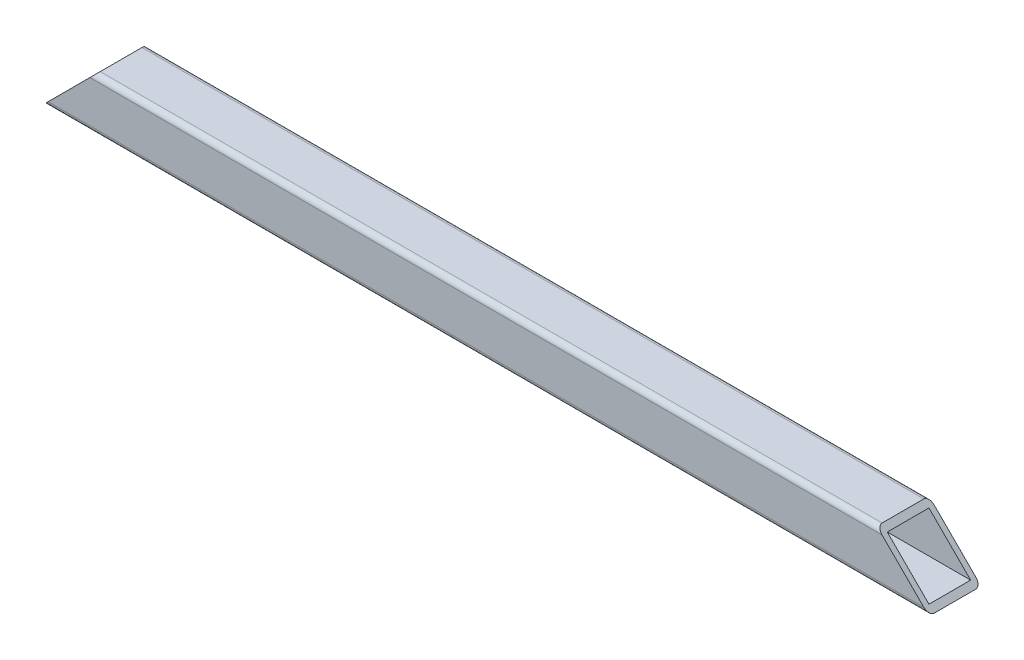
SolidWorks part; units mm, degrees
ref_plane "Front Plane" through (0, 0, 0) normal (0, 0, 1) x (1, 0, 0)
ref_plane "Top Plane" through (0, 0, 0) normal (0, 1, 0) x (1, 0, 0)
ref_plane "Right Plane" through (0, 0, 0) normal (1, 0, 0) x (0, 0, -1)
sketch "Sketch1" plane through (0, 0, 0) normal (0, 0, 1) x (1, 0, 0)
  line L0 (-610.1, -1100) -> (-610.1, 0) construction
  line L1 (-269.9, -1100) -> (-610.1, -1100)
  line L2 (-269.9, -1100) -> (-269.9, -1080)
  line L3 (-269.9, -1080) -> (-610.1, -1080)
  line L4 (-610.1, -1100) -> (-610.1, -1080)
  dimension "D1" = 20
extrude "Boss-Extrude1" add sketch "Sketch1" against normal blind 20
fillet "Fillet1" radius 2 4 edges at (-440, -1080, -20) (-440, -1100, -20) (-440, -1080, 0) (-440, -1100, 0)
sketch "Sketch2" plane through (0, 0, 0) normal (0, 0, 1) x (1, 0, 0)
  line L0 (-269.9, -1100) -> (-269.9, -1080)
  line L1 (-269.9, -1080) -> (-289.9, -1080)
  line L2 (-610.1, -1080) -> (-269.9, -1080) construction
  line L3 (-289.9, -1080) -> (-269.9, -1100)
  line L4 (-610.1, -1100) -> (-590.1, -1080)
  line L5 (-590.1, -1080) -> (-610.1, -1080)
  line L8 (-610.1, -1080) -> (-610.1, -1100)
  dimension "D1" = 45
extrude "Cut-Extrude1" cut sketch "Sketch2" against normal through all
sketch "Sketch3" plane through (0, 0, 0) normal (1, 0, 0) x (0, 0, -1)
  line L8 (18, -1082) -> (2, -1082)
  line L9 (2, -1082) -> (2, -1098)
  line L10 (2, -1098) -> (18, -1098)
  line L11 (18, -1098) -> (18, -1082)
  line L12 (18, -1082) -> (2, -1082)
  line L13 (2, -1082) -> (2, -1098)
  line L14 (2, -1098) -> (18, -1098)
  line L15 (18, -1098) -> (18, -1082)
  dimension "D1" = 2
extrude "Cut-Extrude2" cut sketch "Sketch3" against normal through all
